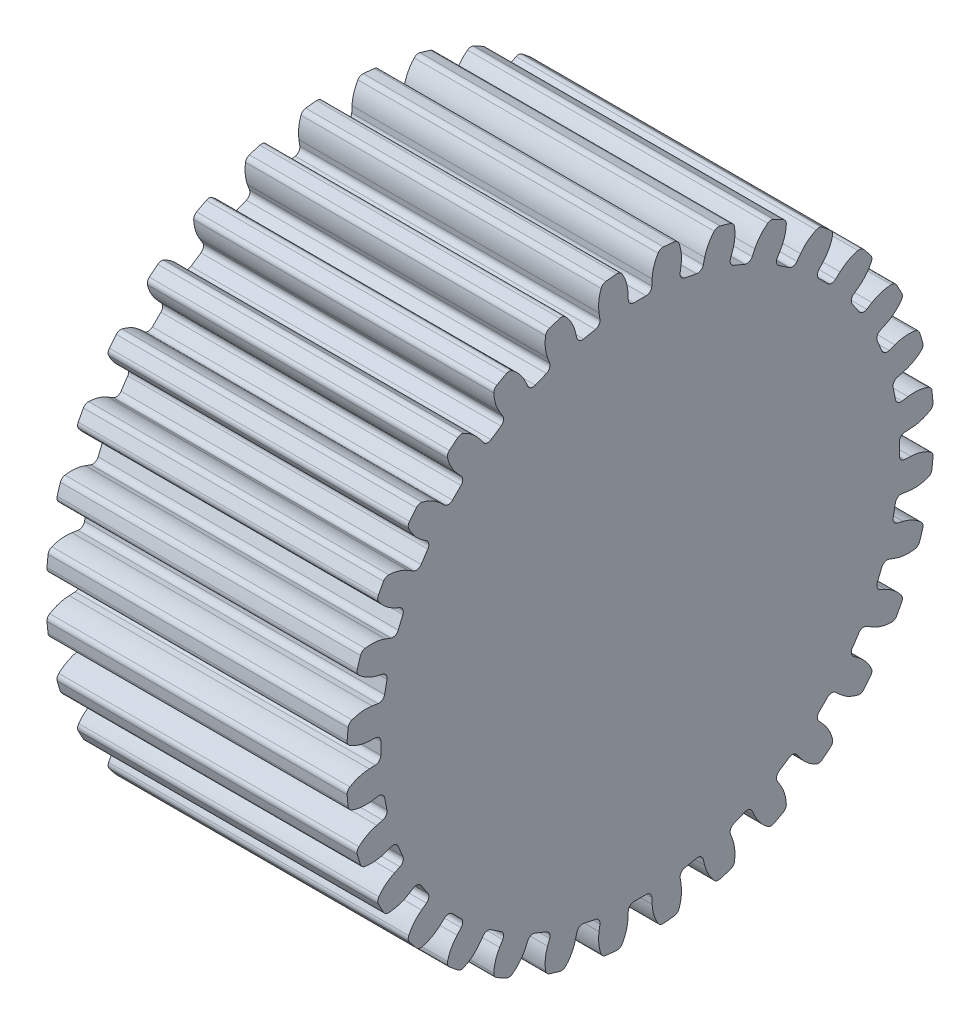
SolidWorks part; units mm, degrees
ref_plane "Plan de face" through (0, 0, 0) normal (0, 0, 1) x (1, 0, 0)
ref_plane "Plan de dessus" through (0, 0, 0) normal (0, 1, 0) x (1, 0, 0)
ref_plane "Plan de droite" through (0, 0, 0) normal (1, 0, 0) x (0, 0, -1)
sketch "Esquisse1" plane through (0, 0, 0) normal (1, 0, 0) x (0, 0, -1)
  circle A0 centre (0, 0) radius 12.73
  dimension "D1" = 25.46
extrude "Extrusion1" add sketch "Esquisse1" along normal blind 13
sketch "Esquisse22" plane through (0, 0, 0) normal (-1, 0, 0) x (0, 0, 1)
  line L0 (0, 0) -> (0, 12.73) construction
  line L1 (-0.5, 11.23) -> (0.5, 11.23)
  line L2 (0.5, 11.23) -> (0.5223, 11.73)
  line L3 (0, 0) -> (-0.5, 11.23) construction
  line L4 (-0.5, 11.23) -> (-0.5223, 11.73)
  line L6 (-0.5223, 11.73) -> (0, 11.73) construction
  line L7 (-0.5223, 11.73) -> (-0.5662, 12.7174) construction
  circle A0 centre (0, 0) radius 12.73 construction
  arc A1 (-0.5223, 11.73) -> (-0.8662, 12.7005) centre (-2.2848, 11.6515) ccw
  arc A2 (-0.8662, 12.7005) -> (0.8662, 12.7005) centre (0, 0) cw
  arc A3 (0.5223, 11.73) -> (0.8662, 12.7005) centre (2.2848, 11.6515) cw
  point P13 (0, 11.23)
  dimension "D1" = 0.3
  dimension "D2" = 0.5
  dimension "D3" = 1.5
  dimension "D4" = 180
  dimension "D6" = 0.5
extrude "Enlèv. mat.-Extru.2" cut sketch "Esquisse22" against normal up to next (13 mm away)
fillet "Congé2" radius 0.25 4 edges at (6.5, 12.7005, 0.8662) (6.5, 11.23, 0.5) (6.5, 11.23, -0.5) (6.5, 12.7005, -0.8662)
pattern_circular "Répétition circulaire1" count 32 over 360 about axis through (0, 0, 0) along (1, 0, 0) of "Enlèv. mat.-Extru.2", "Congé2"
